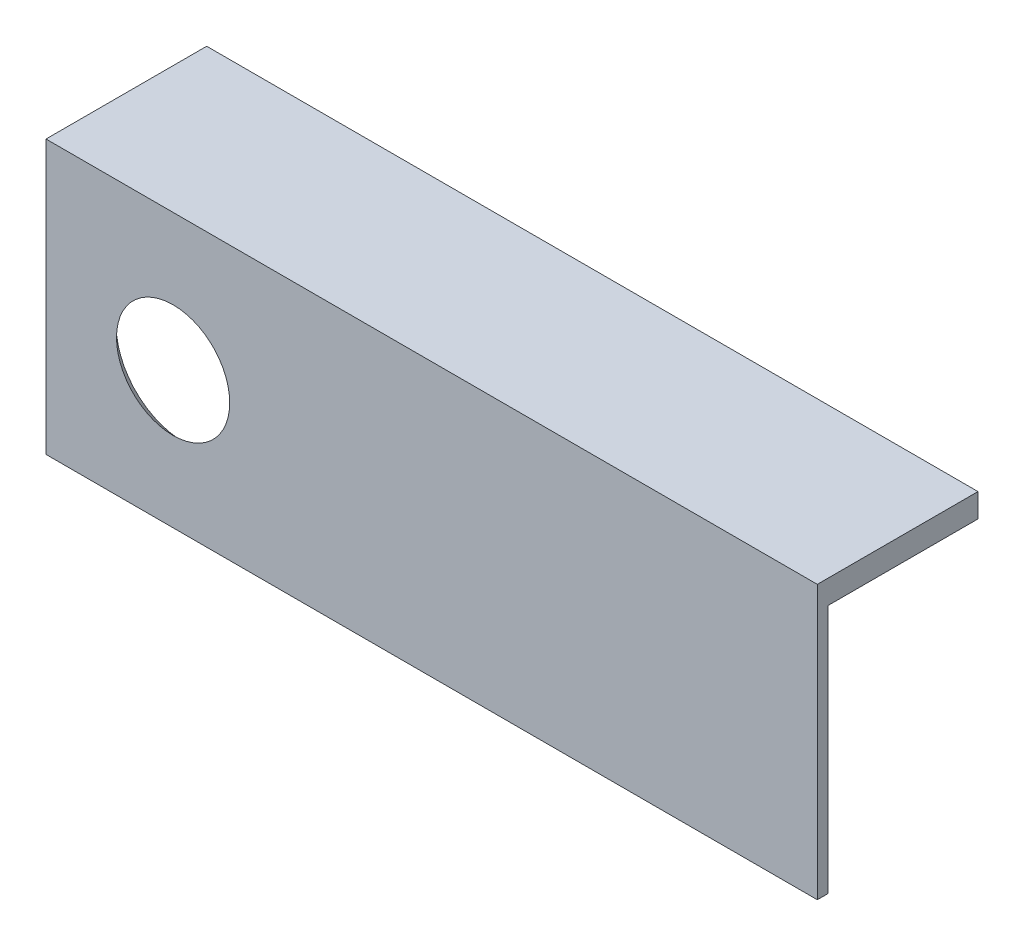
SolidWorks part; units mm, degrees
ref_plane "Alzado" through (0, 0, 0) normal (0, 0, 1) x (1, 0, 0)
ref_plane "Planta" through (0, 0, 0) normal (0, 1, 0) x (1, 0, 0)
ref_plane "Vista lateral" through (0, 0, 0) normal (1, 0, 0) x (0, 0, -1)
sketch "Croquis1" plane through (0, 0, 0) normal (0, 0, 1) x (1, 0, 0)
  line L1 (-24, 8.5) -> (24, 8.5)
  line L2 (-24, 8.5) -> (-24, -8.5)
  line L3 (-24, -8.5) -> (24, -8.5)
  line L4 (24, 8.5) -> (24, -8.5)
  line L5 (-24, 8.5) -> (24, -8.5) construction
  line L6 (-24, -8.5) -> (24, 8.5) construction
  point P0 (0, 0)
  dimension "D1" = 48
  dimension "D2" = 17
extrude "Saliente-Extruir1" add sketch "Croquis1" along normal blind 10
sketch "Croquis2" plane through (0, 0, 10) normal (0, 0, 1) x (1, 0, 0)
  line L0 (0, 16.0015) -> (0, -18.026) construction
  line L1 (-29.4334, 0) -> (28.8105, 0) construction
sketch "Croquis7" plane through (-24, 0, 0) normal (-1, 0, 0) x (0, 0, 1)
  line L0 (0, 7.0242) -> (9.3461, 7.0242)
  line L1 (0, 8.5) -> (0, -8.5) construction
  line L2 (9.3461, 7.0242) -> (9.3461, -8.5)
  line L3 (10, -8.5) -> (0, -8.5) construction
  line L4 (9.3461, -8.5) -> (0, -8.5)
  line L5 (0, -8.5) -> (0, 7.0242)
extrude "Cortar-Extruir1" cut sketch "Croquis7" against normal through all
sketch "Croquis8" plane through (0, 0, 9.3461) normal (0, 0, -1) x (-1, 0, 0)
  line L0 (29.4334, 0) -> (-28.8105, 0) construction
  line L1 (-24, -8.5) -> (-24, 7.0242) construction
  line L2 (24, -8.5) -> (24, 7.0242) construction
  circle A0 centre (-18, 0) radius 3
  circle A1 centre (-9, 0) radius 3
  circle A2 centre (16, 0) radius 4 construction
  dimension "D1" = 6
  dimension "D2" = 9
  dimension "D3" = 8
hole_wizard "Taladro de margen para M3.51" positions "Croquis9" profile "Croquis10" hole size "M3.5" standard "KS" end condition through all
sketch "Croquis9" plane through (0, 0, 9.3461) normal (0, 0, -1) x (-1, 0, 0)
  line L0 (29.4334, 0) -> (-28.8105, 0) construction
  point P0 (16.0903, 0)
sketch "Croquis10" plane through (-16.0903, 0, 9.3461) normal (1, 0, 0) x (0, 1, 0)
  line L0 (0, 0) -> (0, 0.6539)
  line L1 (0, 0.6539) -> (1.95, 0.6539)
  line L2 (1.95, 0.6539) -> (1.95, 2.1728)
  line L3 (1.95, 2.1728) -> (4.2, 0)
  line L5 (4.2, 0) -> (0, 0)
  line L6 (-1.95, 2.1728) -> (-4.2, 0) construction
  line L11 (0, -6.35) -> (0, 107.95) construction
  dimension "Diámetro de taladro hasta el siguiente" = 3.9
  dimension "Profundidad de taladro hasta el siguiente" = 0.6539
  dimension "Diámetro de avellanado cercano" = 8.4
  dimension "Ángulo de avellanado cercano" = 92
